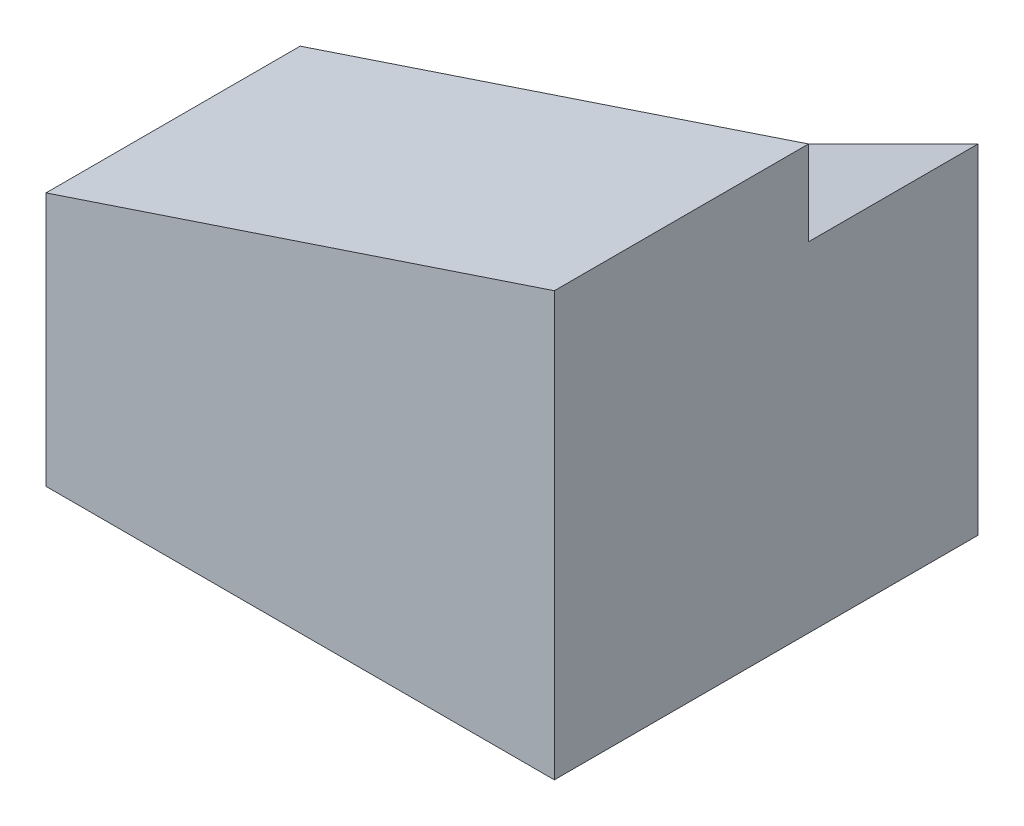
SolidWorks part; units mm, degrees
ref_plane "Front Plane" through (0, 0, 0) normal (0, 0, 1) x (1, 0, 0)
ref_plane "Top Plane" through (0, 0, 0) normal (0, 1, 0) x (1, 0, 0)
ref_plane "Right Plane" through (0, 0, 0) normal (1, 0, 0) x (0, 0, -1)
sketch "Sketch1" plane through (0, 0, 0) normal (0, 0, 1) x (1, 0, 0)
  line L1 (-15, 12.5) -> (15, 12.5)
  line L2 (-15, 12.5) -> (-15, -12.5)
  line L3 (-15, -12.5) -> (15, -12.5)
  line L4 (15, 12.5) -> (15, -12.5)
  line L5 (-15, 12.5) -> (15, -12.5) construction
  line L6 (-15, -12.5) -> (15, 12.5) construction
  point P0 (0, 0)
  dimension "D1" = 30
  dimension "D2" = 25
extrude "Boss-Extrude1" add sketch "Sketch1" along normal blind 25
sketch "Sketch3" plane through (0, 0, 25) normal (0, 0, 1) x (1, 0, 0)
  line L0 (15, 12.5) -> (-15, 2.5)
  line L1 (-15, 12.5) -> (-15, -12.5) construction
  line L2 (-15, 2.5) -> (-15, 12.5)
  line L3 (-15, 12.5) -> (15, 12.5)
  dimension "D1" = 10
extrude "Cut-Extrude1" cut sketch "Sketch3" against normal through all
sketch "Sketch4" plane through (0, 0, 0) normal (0, 0, -1) x (-1, 0, 0)
  line L0 (-15, 12.5) -> (-15, 7.5)
  line L1 (-15, -12.5) -> (-15, 12.5) construction
  line L2 (-15, 7.5) -> (15, -7.5)
  line L3 (15, 2.5) -> (15, -12.5) construction
  line L4 (15, -7.5) -> (15, 2.5)
  line L5 (15, 2.5) -> (-15, 12.5)
  dimension "D1" = 5
  dimension "D2" = 10
extrude "Cut-Extrude2" cut sketch "Sketch4" against normal blind 10
